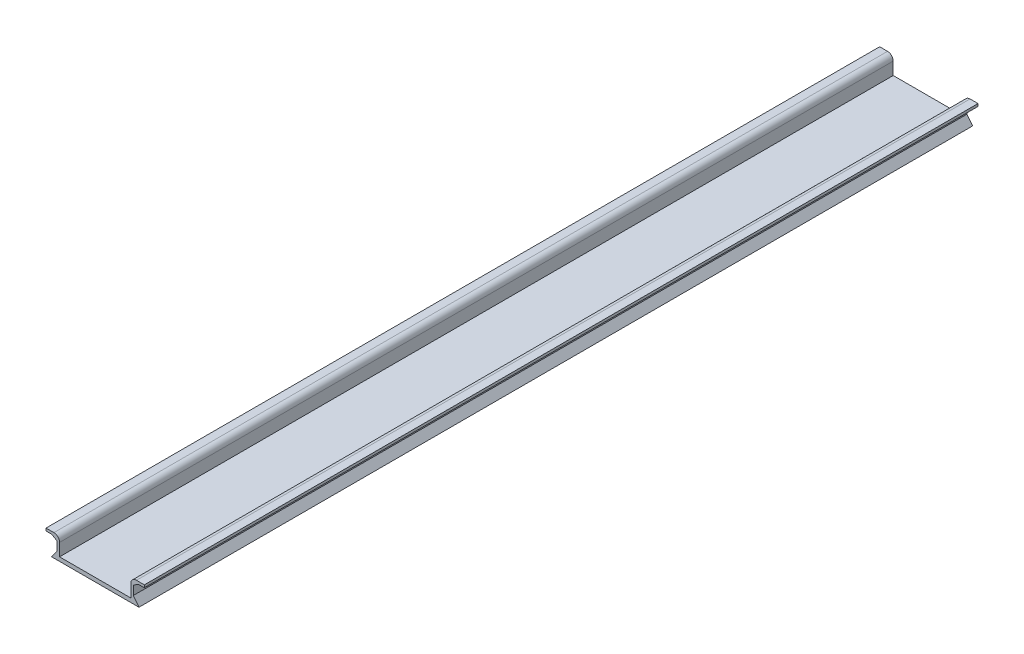
SolidWorks part; units mm, degrees
ref_plane "Front Plane" through (0, 0, 0) normal (0, 0, 1) x (1, 0, 0)
ref_plane "Top Plane" through (0, 0, 0) normal (0, 1, 0) x (1, 0, 0)
ref_plane "Right Plane" through (0, 0, 0) normal (1, 0, 0) x (0, 0, -1)
sketch "Sketch1" plane through (0, 0, 0) normal (0, 0, 1) x (1, 0, 0)
  line L0 (-15.5, 0) -> (15.5, 0)
  line L1 (15.5, 0) -> (13.5, 2.6)
  line L2 (13.5, 2.6) -> (13.5, 5.8)
  line L3 (13.5, 5.8) -> (15.3, 6.92)
  line L4 (15.3, 6.92) -> (17.4, 6.92)
  line L5 (17.4, 6.92) -> (17.4, 7.82)
  line L6 (17.4, 7.82) -> (14.6, 7.82)
  line L7 (12.6, 5.82) -> (12.6, 1.4)
  line L8 (12.6, 1.4) -> (-12.6, 1.4)
  line L9 (0, 1.4) -> (0, 0) construction
  line L10 (-15.5, 0) -> (-13.5, 2.6)
  line L11 (-17.4, 6.92) -> (-17.4, 7.82)
  line L12 (-15.3, 6.92) -> (-17.4, 6.92)
  line L13 (-17.4, 7.82) -> (-14.6, 7.82)
  line L14 (-13.5, 5.8) -> (-15.3, 6.92)
  line L15 (-13.5, 2.6) -> (-13.5, 5.8)
  line L16 (-12.6, 5.82) -> (-12.6, 1.4)
  arc A0 (14.6, 7.82) -> (12.6, 5.82) centre (14.6, 5.82) ccw
  arc A1 (-14.6, 7.82) -> (-12.6, 5.82) centre (-14.6, 5.82) cw
  point P4 (0, 0)
  point P17 (12.6, 7.82)
  dimension "D11" = 2
  dimension "D1" = 31
  dimension "D2" = 1.4
  dimension "D3" = 2.6
  dimension "D4" = 2
  dimension "D5" = 0.9
  dimension "D6" = 0.9
  dimension "D7" = 4.8
  dimension "D8" = 2.1
  dimension "D9" = 7.82
  dimension "D10" = 3.2
extrude "Boss-Extrude1" add sketch "Sketch1" along normal blind 295
